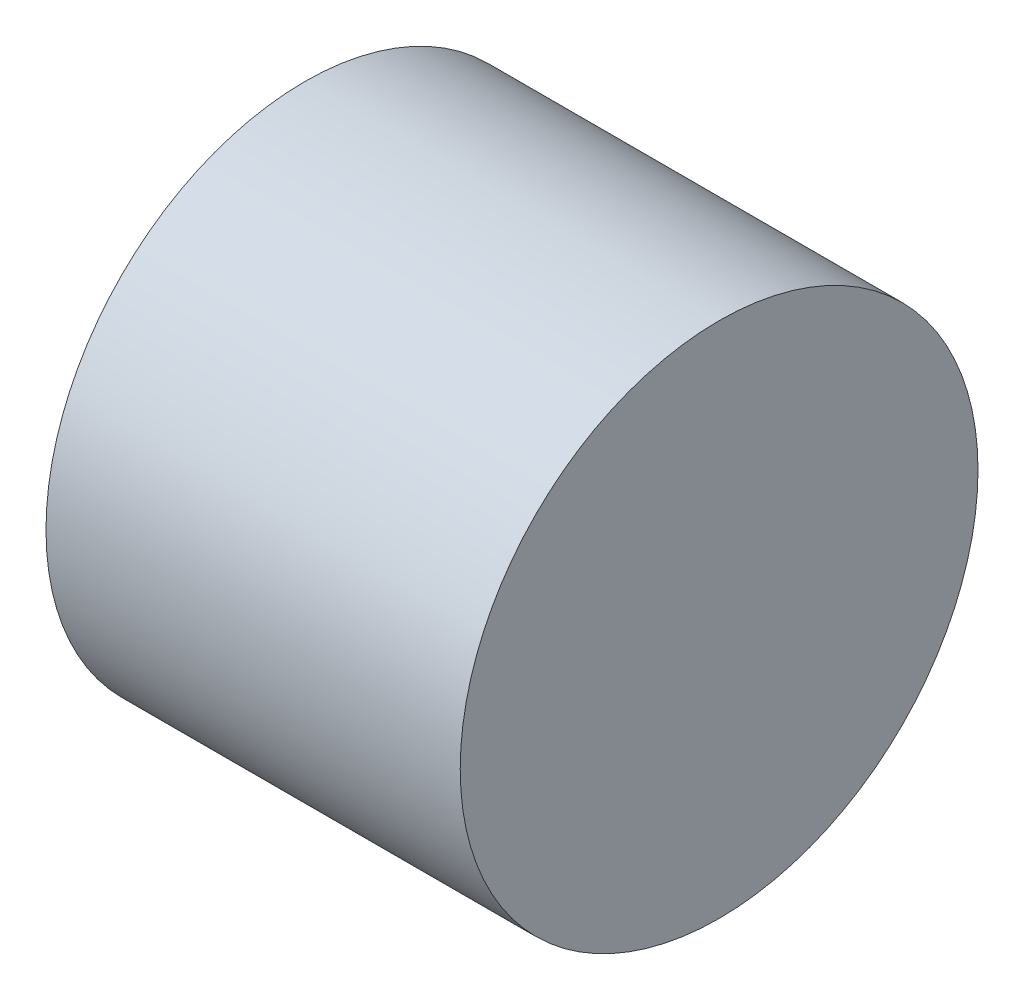
SolidWorks part; units mm, degrees
ref_plane "Front Plane" through (0, 0, 0) normal (0, 0, 1) x (1, 0, 0)
ref_plane "Top Plane" through (0, 0, 0) normal (0, 1, 0) x (1, 0, 0)
ref_plane "Right Plane" through (0, 0, 0) normal (1, 0, 0) x (0, 0, -1)
sketch "Sketch1" plane through (0, 0, 0) normal (1, 0, 0) x (0, 0, -1)
  circle A0 centre (0, 0) radius 25
extrude "Boss-Extrude1" add sketch "Sketch1" along normal blind 40
